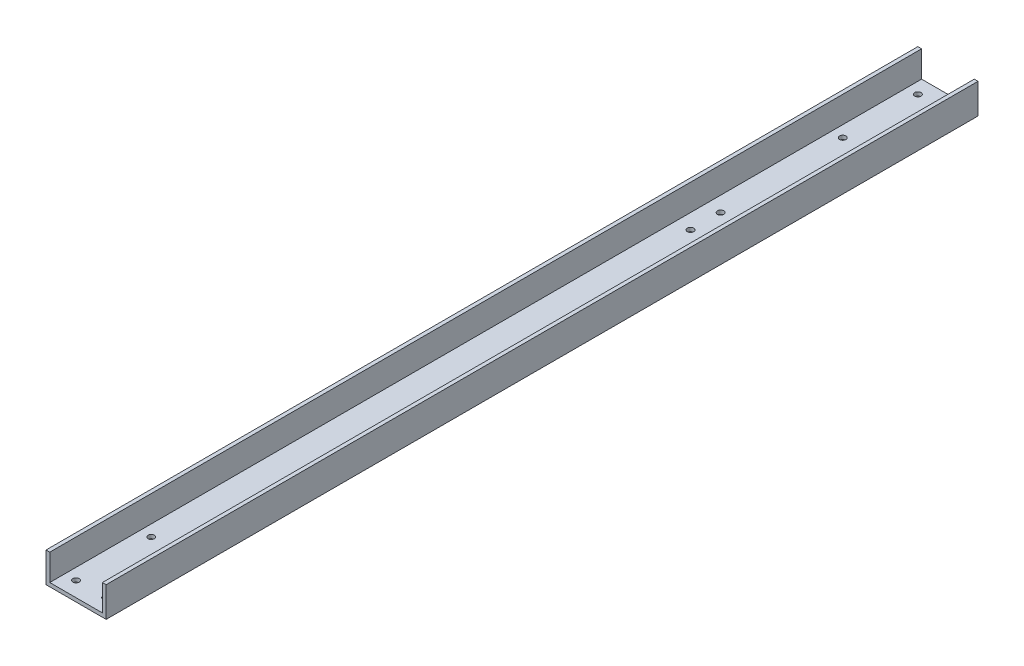
SolidWorks part; units mm, degrees
ref_plane "Front Plane" through (0, 0, 0) normal (0, 0, 1) x (1, 0, 0)
ref_plane "Top Plane" through (0, 0, 0) normal (0, 1, 0) x (1, 0, 0)
ref_plane "Right Plane" through (0, 0, 0) normal (1, 0, 0) x (0, 0, -1)
sketch "Sketch1" plane through (0, 0, 0) normal (0, 0, 1) x (1, 0, 0)
  line L0 (3.175, 3.175) -> (3.175, 25.4)
  line L1 (0, 0) -> (50.8, 0)
  line L2 (0, 0) -> (0, 25.4)
  line L3 (3.175, 3.175) -> (47.625, 3.175)
  line L4 (50.8, 0) -> (50.8, 25.4)
  line L5 (47.625, 3.175) -> (47.625, 25.4)
  line L6 (0, 25.4) -> (3.175, 25.4)
  line L7 (47.625, 25.4) -> (50.8, 25.4)
  dimension "D1" = 25.4
  dimension "D2" = 50.8
  dimension "D3" = 3.175
extrude "f" add sketch "Sketch1" along normal blind 736.6
sketch "Sketch2" plane through (0, 3.175, 0) normal (0, 1, 0) x (1, 0, 0)
  line L0 (15.5889, -736.6) -> (15.5889, -723.9) construction
  line L1 (12.7, -723.9) -> (38.1, -723.9) construction
  line L2 (12.7, -723.9) -> (12.7, -660.4) construction
  line L3 (12.7, -660.4) -> (38.1, -660.4) construction
  line L4 (38.1, -723.9) -> (38.1, -660.4) construction
  line L5 (12.7, -723.9) -> (38.1, -660.4) construction
  line L6 (12.7, -660.4) -> (38.1, -723.9) construction
  line L7 (47.625, -736.6) -> (3.175, -736.6) construction
  line L8 (3.175, -701.3254) -> (12.7, -701.3254) construction
  line L9 (3.175, -736.6) -> (3.175, 0) construction
  line L10 (38.1, -681.1466) -> (47.625, -681.1466) construction
  line L11 (47.625, -736.6) -> (47.625, 0) construction
  line L12 (3.175, -368.3) -> (47.625, -368.3) construction
  circle A0 centre (12.7, -723.9) radius 2.667
  circle A1 centre (12.7, -660.4) radius 2.667
  circle A2 centre (38.1, -660.4) radius 2.667
  circle A3 centre (38.1, -723.9) radius 2.667
  circle A4 centre (38.1, -12.7) radius 2.667
  circle A5 centre (38.1, -76.2) radius 2.667
  circle A6 centre (12.7, -12.7) radius 2.667
  circle A7 centre (12.7, -76.2) radius 2.667
  point P4 (25.4, -692.15)
  dimension "D4" = 5.334
  dimension "D1" = 25.4
  dimension "D2" = 63.5
  dimension "D3" = 12.7
extrude "Cut-Extrude1" cut sketch "Sketch2" against normal up to next
sketch "Sketch3" plane through (0, 3.175, 0) normal (0, 1, 0) x (1, 0, 0)
  circle A0 centre (34.925, -207.9371) radius 2.667 construction
  circle A1 centre (34.925, -207.9371) radius 2.667
  circle A2 centre (15.875, -207.9371) radius 2.667 construction
  circle A3 centre (15.875, -207.9371) radius 2.667
  circle A4 centre (34.925, -182.5371) radius 2.667 construction
  circle A5 centre (34.925, -182.5371) radius 2.667
  circle A6 centre (15.875, -182.5371) radius 2.667 construction
  circle A7 centre (15.875, -182.5371) radius 2.667
extrude "Cut-Extrude2" cut sketch "Sketch3" against normal up to next
